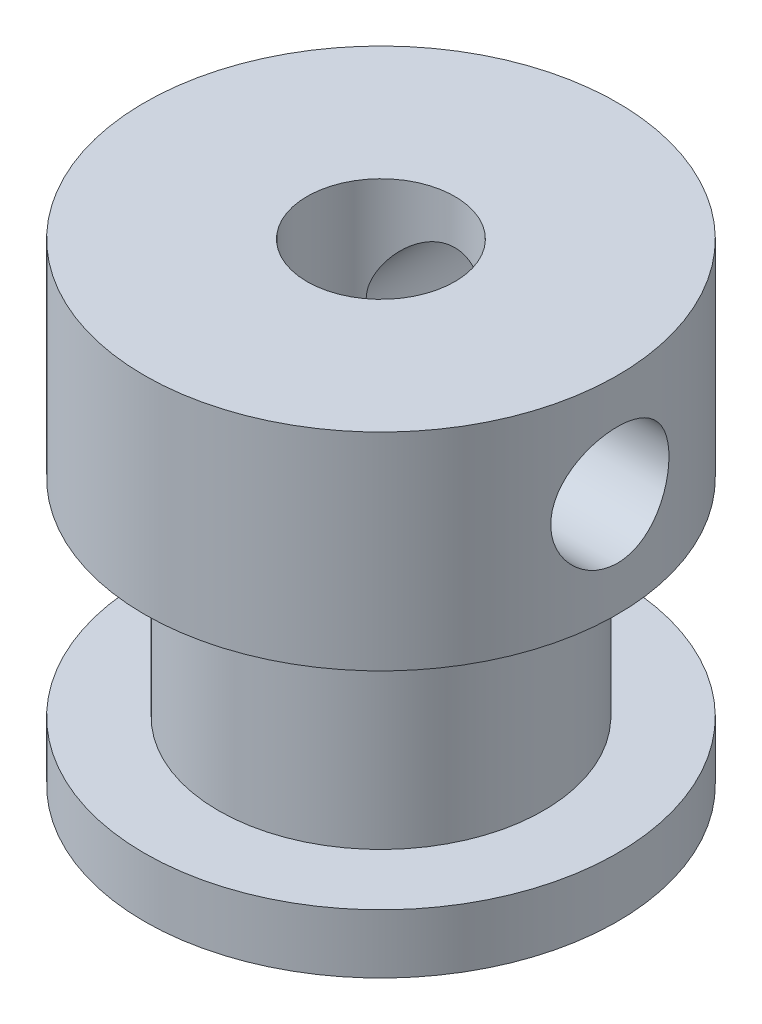
SolidWorks part; units mm, degrees
ref_plane "Front Plane" through (0, 0, 0) normal (0, 0, 1) x (1, 0, 0)
ref_plane "Top Plane" through (0, 0, 0) normal (0, 1, 0) x (1, 0, 0)
ref_plane "Right Plane" through (0, 0, 0) normal (1, 0, 0) x (0, 0, -1)
sketch "Sketch1" plane through (0, 0, 0) normal (0, 1, 0) x (1, 0, 0)
  circle A0 centre (0, 0) radius 8
  dimension "D1" = 16
extrude "Boss-Extrude1" add sketch "Sketch1" along normal blind 2
sketch "Sketch2" plane through (0, 2, 0) normal (0, 1, 0) x (1, 0, 0)
  circle A0 centre (0, 0) radius 5.5
  dimension "D1" = 11
extrude "Boss-Extrude2" add sketch "Sketch2" along normal blind 7
sketch "Sketch3" plane through (0, 9, 0) normal (0, 1, 0) x (1, 0, 0)
  circle A0 centre (0, 0) radius 8
  dimension "D1" = 16
extrude "Boss-Extrude3" add sketch "Sketch3" along normal blind 7
sketch "Sketch4" plane through (0, 16, 0) normal (0, 1, 0) x (1, 0, 0)
  circle A0 centre (0, 0) radius 2.5
  dimension "D1" = 5
extrude "Cut-Extrude2" cut sketch "Sketch4" against normal through all
sketch "Sketch7" plane through (0, 0, 0) normal (0, 0, 1) x (1, 0, 0)
  line L0 (8, 16) -> (-8, 16) construction
  circle A0 centre (0, 12.5) radius 2
  point P5 (0, 0)
  point P6 (0, 0)
  dimension "D2" = 4
  dimension "D1" = 3.5
extrude "Cut-Extrude3" cut sketch "Sketch7" against normal through all
pattern_circular "CirPattern1" count 2 every 90 about axis through (0, 16, 0) along (0, -1, 0) of "Cut-Extrude3"
